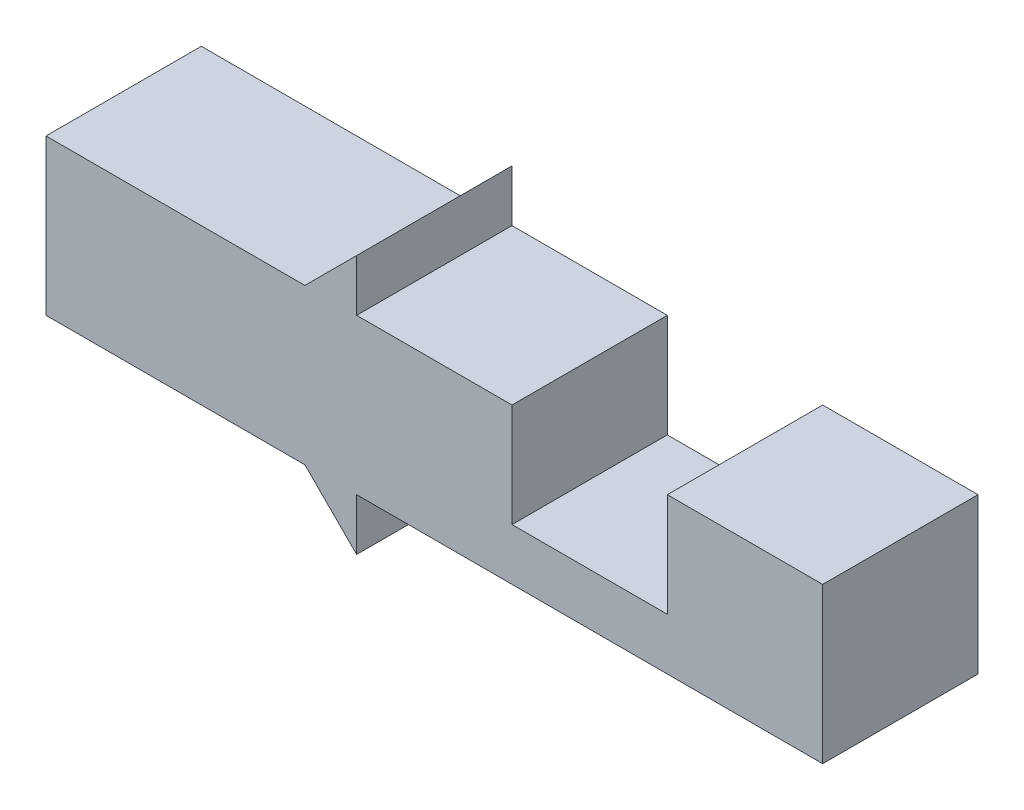
SolidWorks part; units mm, degrees
ref_plane "정면" through (0, 0, 0) normal (0, 0, 1) x (1, 0, 0)
ref_plane "윗면" through (0, 0, 0) normal (0, 1, 0) x (1, 0, 0)
ref_plane "우측면" through (0, 0, 0) normal (1, 0, 0) x (0, 0, -1)
sketch "Sketch1" plane through (0, 0, 0) normal (0, 0, 1) x (1, 0, 0)
  line L0 (0, 37.9579) -> (0, -40.1053) construction
  line L16 (0, 0) -> (-18, 0)
  line L17 (-18, 0) -> (-18, -2)
  line L18 (-18, -2) -> (-20, 0)
  line L19 (-20, 0) -> (-30, 0)
  line L20 (-30, 0) -> (-30, 6)
  line L21 (-30, 6) -> (-20, 6)
  line L22 (-20, 6) -> (-18, 8)
  line L23 (-18, 8) -> (-18, 6)
  line L24 (-18, 6) -> (-12, 6)
  line L25 (-12, 6) -> (-12, 2)
  line L26 (-12, 2) -> (-6, 2)
  line L27 (-6, 2) -> (-6, 6)
  line L28 (-6, 6) -> (0, 6)
  line L29 (0, 6) -> (0, 0)
  point P17 (-22.8904, 6)
  dimension "D1" = 6
  dimension "D2" = 30
  dimension "D3" = 2
  dimension "D4" = 2
  dimension "D5" = 6
  dimension "D6" = 2
  dimension "D7" = 2
  dimension "D8" = 6
  dimension "D9" = 4
  dimension "D10" = 6
  dimension "D11" = 6
extrude "Boss-Extrude1" add sketch "Sketch1" along normal blind 6
